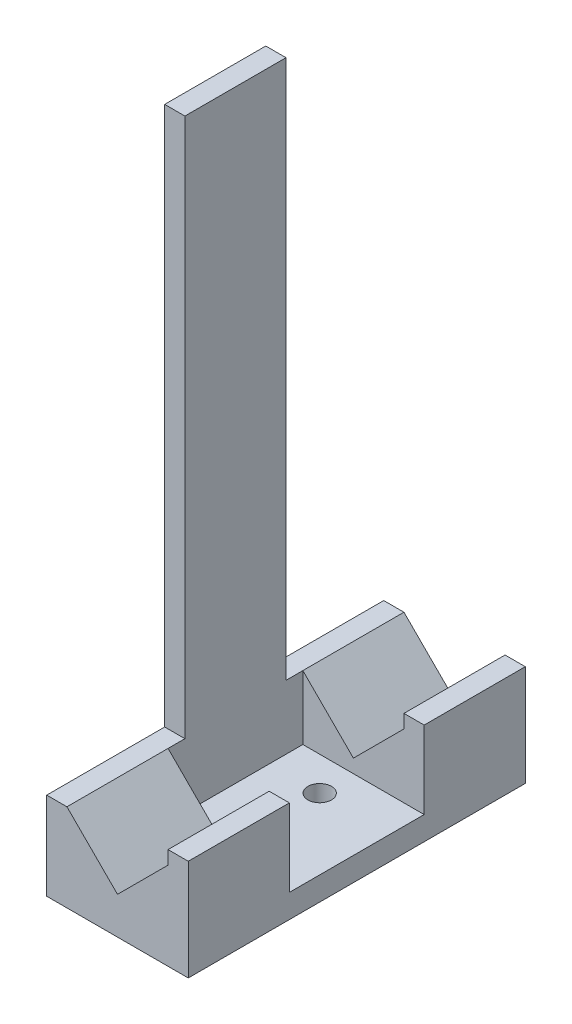
SolidWorks part; units mm, degrees
ref_plane "Plano frontal" through (0, 0, 0) normal (0, 0, 1) x (1, 0, 0)
ref_plane "Plano superior" through (0, 0, 0) normal (0, 1, 0) x (1, 0, 0)
ref_plane "Plano direito" through (0, 0, 0) normal (1, 0, 0) x (0, 0, -1)
sketch "Esboço1" plane through (0, 0, 0) normal (0, 0, 1) x (1, 0, 0)
  line L0 (21, 0) -> (0, 0)
  line L1 (21, 0) -> (21, 15)
  line L2 (18, 13) -> (18, 15)
  line L3 (18, 13) -> (10.5, 5.5)
  line L4 (10.5, 5.5) -> (3, 13)
  line L5 (18, 15) -> (21, 15)
  line L6 (3, 13) -> (3, 93)
  line L7 (3, 93) -> (0, 93)
  line L8 (0, 93) -> (0, 8.5)
  line L9 (-3, 1) -> (-2, 1)
  line L10 (-3, 1) -> (-3, 4)
  line L11 (-3, 4) -> (0, 8.5)
  line L12 (-2, 1) -> (0, 4)
  line L13 (0, 4) -> (0, 0)
  point P0 (0, 0)
  dimension "D1" = 2
  dimension "D2" = 15
  dimension "D3" = 15
  dimension "D4" = 3
  dimension "D5" = 3
  dimension "D6" = 1
  dimension "D7" = 45
  dimension "D8" = 80
  dimension "D9" = 3
  dimension "D10" = 1
extrude "Ressalto-extrusão1" add sketch "Esboço1" along normal blind 50
sketch "Esboço3" plane through (0, 93, 0) normal (0, 1, 0) x (1, 0, 0)
  line L0 (3, -50) -> (3, 0) construction
  line L1 (-3, 0) -> (3, 0)
  line L2 (-3, 0) -> (-3, -17.5)
  line L3 (-3, -17.5) -> (3, -17.5)
  line L4 (3, 0) -> (3, -17.5)
  line L5 (0, -25) -> (3, -25) construction
  line L6 (0, -50) -> (0, 0) construction
  line L7 (3, -50) -> (3, 0) construction
  line L8 (3, -50) -> (3, -32.5)
  line L9 (-3, -32.5) -> (3, -32.5)
  line L10 (-3, -50) -> (-3, -32.5)
  line L11 (-3, -50) -> (3, -50)
  point P17 (-3, 0)
  dimension "D1" = 15
extrude "Corte-extrusão2" cut sketch "Esboço3" against normal up to vertex (80 mm away)
sketch "Esboço4" plane through (21, 0, 0) normal (1, 0, 0) x (0, 0, -1)
  line L0 (-50, 15) -> (0, 15) construction
  line L1 (-35, 15) -> (-15, 15)
  line L2 (-35, 15) -> (-35, 3.5)
  line L3 (-35, 3.5) -> (-15, 3.5)
  line L4 (-15, 15) -> (-15, 3.5)
  line L5 (-25, 0) -> (-25, 45.0761) construction
  line L6 (-50, 0) -> (0, 0) construction
  dimension "D1" = 3.5
  dimension "D2" = 20
extrude "Corte-extrusão3" cut sketch "Esboço4" against normal up to surface (18 mm away) up to face at (3, 53, 25)
sketch "Esboço5" plane through (0, 3.5, 0) normal (0, 1, 0) x (1, 0, 0)
  line L0 (3, -25) -> (21, -25) construction
  line L1 (3, -32.5) -> (3, -17.5) construction
  line L2 (21, -35) -> (21, -15) construction
  line L3 (0, -50) -> (0, 0) construction
  line L4 (-3, 0) -> (0, 0)
  line L5 (-3, 0) -> (-3, -22.5)
  line L6 (-3, -22.5) -> (0, -22.5)
  line L7 (0, 0) -> (0, -22.5)
  line L8 (-3, -27.5) -> (0, -27.5)
  line L9 (0, -50) -> (0, -27.5)
  line L10 (-3, -50) -> (0, -50)
  line L11 (-3, -50) -> (-3, -27.5)
  circle A0 centre (10.5, -20) radius 1.75
  circle A1 centre (10.5, -30) radius 1.75
  dimension "D1" = 3.5
  dimension "D2" = 10
  dimension "D3" = 5
extrude "Corte-extrusão4" cut sketch "Esboço5" against normal through all both and the other way through all
